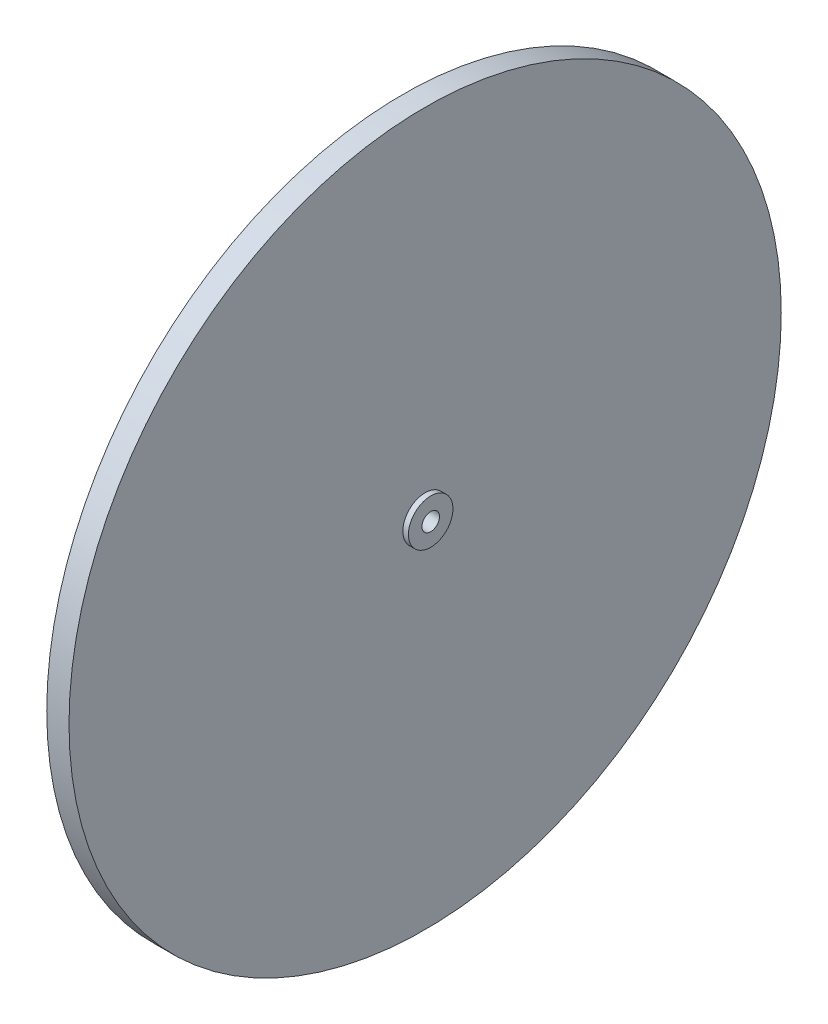
SolidWorks part; units mm, degrees
ref_plane "Front Plane" through (0, 0, 0) normal (0, 0, 1) x (1, 0, 0)
ref_plane "Top Plane" through (0, 0, 0) normal (0, 1, 0) x (1, 0, 0)
ref_plane "Right Plane" through (0, 0, 0) normal (1, 0, 0) x (0, 0, -1)
sketch "Sketch1" plane through (0, 0, 0) normal (0, 0, 1) x (1, 0, 0)
  line L0 (0, 0) -> (9.525, 0) construction
  line L1 (0, 6.35) -> (1.5875, 6.35)
  line L2 (1.5875, 6.35) -> (1.5875, 101.6)
  line L3 (1.5875, 101.6) -> (7.9375, 101.6)
  line L4 (7.9375, 101.6) -> (7.9375, 6.35)
  line L5 (7.9375, 6.35) -> (9.525, 6.35)
  line L6 (9.525, 6.35) -> (9.525, 2.5)
  line L7 (9.525, 2.5) -> (0, 2.5)
  line L8 (0, 2.5) -> (0, 6.35)
  dimension "D1" = 12.7
  dimension "D2" = 5
  dimension "D3" = 9.525
  dimension "D4" = 6.35
  dimension "D5" = 203.2
revolve "Revolve1" add sketch "Sketch1" angle 360 about L0
